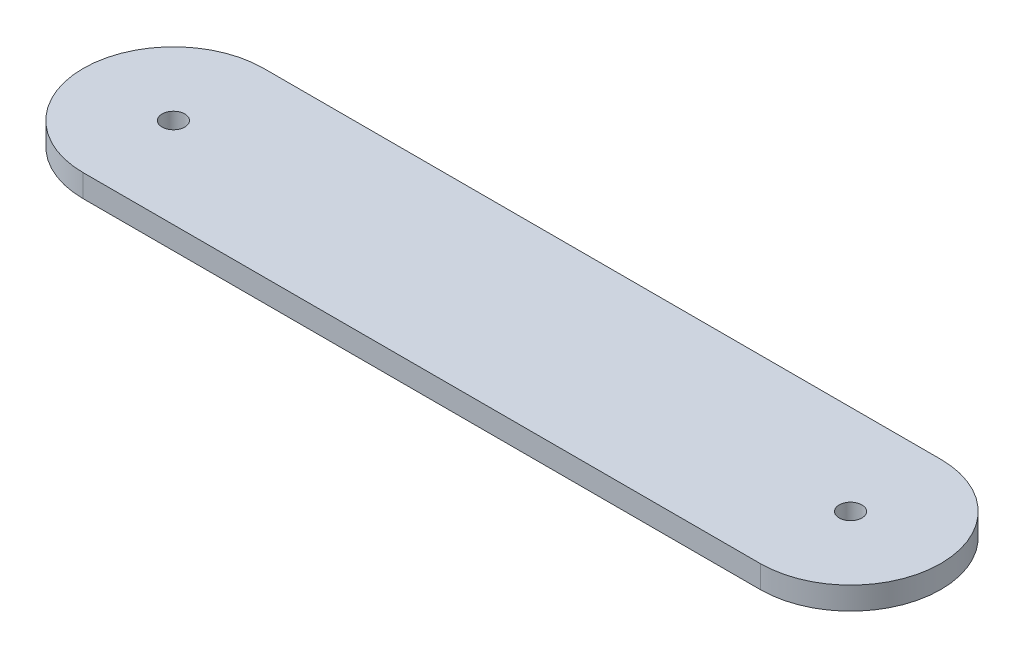
SolidWorks part; units mm, degrees
ref_plane "Front Plane" through (0, 0, 0) normal (0, 0, 1) x (1, 0, 0)
ref_plane "Top Plane" through (0, 0, 0) normal (0, 1, 0) x (1, 0, 0)
ref_plane "Right Plane" through (0, 0, 0) normal (1, 0, 0) x (0, 0, -1)
sketch "Sketch1" plane through (0, 0, 0) normal (0, 1, 0) x (1, 0, 0)
  line L0 (-47.625, 0) -> (47.625, 0) construction
  line L1 (-47.625, 12.7) -> (47.625, 12.7)
  line L2 (-47.625, -12.7) -> (47.625, -12.7)
  arc A0 (-47.625, 12.7) -> (-47.625, -12.7) centre (-47.625, 0) ccw
  arc A1 (47.625, -12.7) -> (47.625, 12.7) centre (47.625, 0) ccw
  point P3 (0, 0)
  dimension "D2" = 12.7
  dimension "D1" = 95.25
extrude "Boss-Extrude1" add sketch "Sketch1" along normal blind 3.175
hole_wizard "M3 Clearance Hole1" positions "Sketch2" profile "Sketch3" hole size "M3" standard "ANSI Metric" end condition through all
sketch "Sketch2" plane through (0, 3.175, 0) normal (0, 1, 0) x (1, 0, 0)
  point P0 (-47.625, 0)
  point P3 (47.625, 0)
sketch "Sketch3" plane through (-47.625, 3.175, 0) normal (1, 0, 0) x (0, 0, 1)
  line L0 (0, 0) -> (0, 3.175)
  line L1 (0, 3.175) -> (1.6, 3.175)
  line L2 (1.6, 3.175) -> (1.6, 0)
  line L5 (1.6, 0) -> (0, 0)
  line L11 (0, -6.35) -> (0, 107.95) construction
  dimension "Thru Hole Dia." = 3.2
  dimension "Thru Hole Depth" = 3.175
